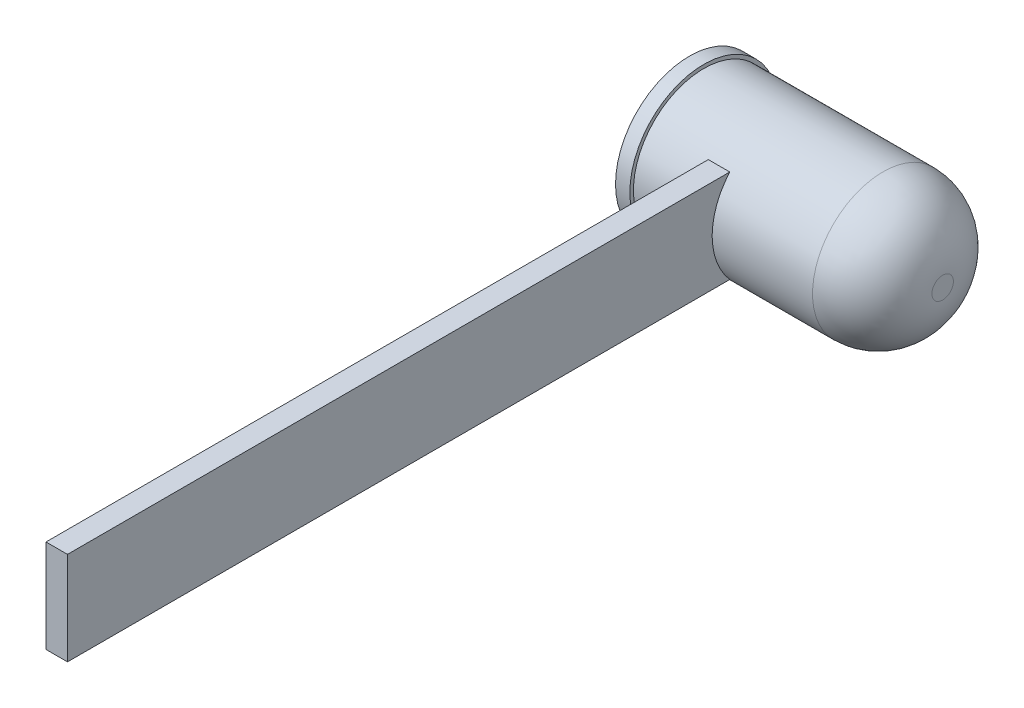
SolidWorks part; units mm, degrees
material "Aleación 1060"
ref_plane "Alzado" through (0, 0, 0) normal (0, 0, 1) x (1, 0, 0)
ref_plane "Planta" through (0, 0, 0) normal (0, 1, 0) x (1, 0, 0)
ref_plane "Vista lateral" through (0, 0, 0) normal (1, 0, 0) x (0, 0, -1)
sketch "Croquis1" plane through (0, 0, 0) normal (1, 0, 0) x (0, 0, -1)
  circle A0 centre (0, 0) radius 2.95
  dimension "D1" = 5.9
extrude "Saliente-Extruir1" add sketch "Croquis1" along normal blind 10
fillet "Redondeo1" radius 2.5 1 edges at (10, 0, -2.95)
sketch "Croquis2" plane through (0, 0, 0) normal (-1, 0, 0) x (0, 0, 1)
  circle A0 centre (0, 0) radius 3.1
  dimension "D1" = 6.2
extrude "Saliente-Extruir2" add sketch "Croquis2" along normal blind 0.6
sketch3d "Croquis3D1"
  point P0 (2.469, 0.296, -2.9351)
sketch3d "Croquis3D2"
  point P0 (3.5989, 0.0626, 2.9493)
ref_plane "Plano2" through (0, 0, 2.9493) normal (0, 0, 1) x (1, 0, 0)
sketch "Croquis5" plane through (0, 0, 2.9493) normal (0, 0, 1) x (1, 0, 0)
  line L0 (2.4978, 2.95) -> (2.4978, -2.95) construction
  line L1 (7.5, 2.95) -> (0, 2.95) construction
  line L2 (0, -2.95) -> (7.5, -2.95) construction
  line L3 (2.4978, 0) -> (3.3987, 0) construction
  line L4 (2.3987, -1.95) -> (2.3987, 1.95)
  line L5 (2.3987, 1.95) -> (3.2987, 1.95)
  line L6 (3.2987, 1.95) -> (3.2987, -1.95)
  line L7 (3.2987, -1.95) -> (2.3987, -1.95)
  point P12 (2.3987, 0)
  dimension "D1" = 3.9
  dimension "D2" = 0.9
extrude "Saliente-Extruir4" add sketch "Croquis5" along normal blind 27
sketch "Croquis8" plane through (0, 0, 2.9493) normal (0, 0, -1) x (-1, 0, 0)
  line L1 (-2.3987, 1.95) -> (-3.2987, 1.95)
  line L2 (-2.3987, 1.95) -> (-2.3987, -1.95)
  line L3 (-2.3987, -1.95) -> (-3.2987, -1.95)
  line L4 (-3.2987, 1.95) -> (-3.2987, -1.95)
extrude "Saliente-Extruir5" add sketch "Croquis8" along normal blind 2
